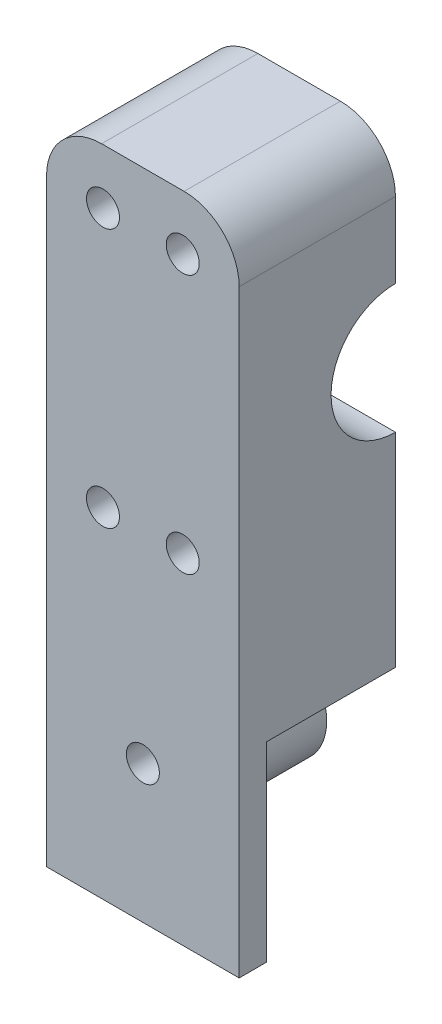
SolidWorks part; units mm, degrees
material "Nylon 6/10"
ref_plane "Front Plane" through (0, 0, 0) normal (0, 0, 1) x (1, 0, 0)
ref_plane "Top Plane" through (0, 0, 0) normal (0, 1, 0) x (1, 0, 0)
ref_plane "Right Plane" through (0, 0, 0) normal (1, 0, 0) x (0, 0, -1)
sketch "Sketch1" plane through (0, 0, 0) normal (1, 0, 0) x (0, 0, -1)
  line L1 (-28.4, -59.4) -> (-23.4, -59.4)
  line L2 (-28.4, -59.4) -> (-28.4, 59.4) construction
  line L3 (-28.4, 59.4) -> (28.4, 59.4)
  line L4 (28.4, -59.4) -> (28.4, 59.4) construction
  line L5 (-28.4, -59.4) -> (28.4, 59.4) construction
  line L6 (-28.4, 59.4) -> (28.4, -59.4) construction
  line L7 (28.4, 59.4) -> (28.4, -59.4)
  line L8 (-28.4, 59.4) -> (-28.4, -59.4)
  line L9 (-28.4, -14.4) -> (28.4, -14.4) construction
  line L10 (23.4, -59.4) -> (28.4, -59.4)
  line L11 (-23.4, -14.4) -> (23.4, -14.4)
  line L12 (-23.4, -14.4) -> (-23.4, -59.4)
  line L14 (23.4, -14.4) -> (23.4, -59.4)
  circle A0 centre (0, 24) radius 12.7 construction
  circle A1 centre (0, 24) radius 11.7
  point P0 (0, 0)
  dimension "D3" = 25.4
  dimension "D7" = 5
  dimension "D2" = 73.8
  dimension "D8" = 1
  dimension "D1" = 56.8
  dimension "D4" = 35.4
  dimension "D5" = 45
  dimension "D6" = 5
extrude "Boss-Extrude1" add sketch "Sketch1" along normal blind 35
sketch "Sketch2" plane through (0, 0, 28.4) normal (0, 0, 1) x (1, 0, 0)
  line L0 (35, -59.4) -> (0, -59.4) construction
  line L1 (0, -14.4) -> (35, -14.4) construction
  line L3 (0, -24.7175) -> (0, -13.4)
  line L4 (0, -59.4) -> (0, 59.4) construction
  line L6 (35, 59.4) -> (35, -59.4) construction
  line L7 (35, -13.4) -> (35, -24.7175)
  line L8 (0, -13.4) -> (35, -13.4)
  line L9 (0, 59.4) -> (0, -59.4) construction
  circle A0 centre (17.5, -34.4) radius 10
  arc A3 (35, -24.7175) -> (0, -24.7175) centre (17.5, -34.4) ccw
  point P4 (17.5, -59.4)
  dimension "D1" = 20
  dimension "D2" = 20
  dimension "D3" = 1
extrude "Boss-Extrude3" add sketch "Sketch2" against normal up to surface (51.8 mm away) up to face at (17.5, -36.9, -23.4)
sketch "Sketch3" plane through (0, 0, 28.4) normal (0, 0, 1) x (1, 0, 0)
  line L0 (0, 59.4) -> (0, -59.4) construction
  line L1 (35, 59.4) -> (0, 59.4) construction
  line L2 (35, 59.4) -> (35, -59.4) construction
  circle A0 centre (10.25, 49.4) radius 3
  circle A1 centre (17.5, -34.4) radius 3
  circle A2 centre (10.25, 2.3) radius 3
  circle A3 centre (24.75, 2.3) radius 3
  circle A4 centre (24.75, 49.4) radius 3
  dimension "D1" = 6
  dimension "D2" = 10
  dimension "D5" = 47.1
  dimension "D3" = 10.25
  dimension "D4" = 10.25
extrude "Cut-Extrude1" cut sketch "Sketch3" against normal through all both and the other way through all
ref_plane "Plane2" through (12.7375, 0, 0) normal (-1, 0, 0) x (0, 0, 1)
sketch "Sketch6" plane through (35, 0, 0) normal (1, 0, 0) x (0, 0, -1)
  line L0 (28.4, 59.4) -> (-28.4, 59.4) construction
  line L1 (0, 59.4) -> (28.4, 59.4)
  line L2 (0, 59.4) -> (0, -59.4)
  line L3 (0, -59.4) -> (28.4, -59.4)
  line L4 (28.4, 59.4) -> (28.4, -59.4)
extrude "Cut-Extrude3" cut sketch "Sketch6" against normal through all
sketch "Sketch7" plane through (0, 0, 0) normal (0, 0, -1) x (-1, 0, 0)
  line L0 (0, 59.4) -> (-35, 59.4) construction
  line L1 (-35, 59.4) -> (-35, 35.7) construction
  line L2 (0, 12.3) -> (-35, 12.3) construction
  circle A0 centre (-24.75, 49.4) radius 4
  circle A1 centre (-10.25, 49.4) radius 4
  circle A2 centre (-24.75, 2.3) radius 4
  circle A3 centre (-10.25, 2.3) radius 4
  circle A7 centre (-24.75, 49.4) radius 3
  circle A8 centre (-10.25, 49.4) radius 3
  circle A9 centre (-10.25, 2.3) radius 3
  circle A10 centre (-24.75, 2.3) radius 3
  dimension "D1" = 14.5
  dimension "D3" = 8
  dimension "D4" = 6
  dimension "D6" = 10
  dimension "D2" = 10
  dimension "D5" = 10.25
  dimension "D7" = 14.5
sketch "Sketch8" plane through (0, 0, 0) normal (0, 0, -1) x (-1, 0, 0)
  circle A0 centre (-17.5, -34.4) radius 10
  circle A1 centre (-17.5, -34.4) radius 3
  circle A2 centre (-17.5, -34.4) radius 10 construction
  circle A3 centre (-17.5, -34.4) radius 3 construction
extrude "Cut-Extrude4" cut sketch "Sketch8" against normal blind 5
extrude "Cut-Extrude5" cut sketch "Sketch7" against normal blind 5
fillet "Fillet1" radius 10 2 edges at (35, 59.4, 14.2) (0, 59.4, 14.2)
equation "\"keelOutDiameter\"= 1in"
equation "\"keelInDiameter\"= \"keelOutDiameter\" - 0.125in"
equation "\"frontBoltClearance\"= 7.25mm"
equation "\"betweenBoltsDistance\"= 20mm"
equation "\"wingLength\"= 1.4m"
equation "\"frontTubeLength\"= \"wingLength\" / sin ( 34.95deg )"
equation "\"plateThickness\"= 5mm"
equation "\"crossBarOutDiameter\"= 1in"
equation "\"crossBarInDiameter\"= \"crossBarOutDiameter\" - 0.125in"
equation "\"frontToCrossBar\"= 466mm"
equation "\"D3@Sketch1\"=\"keelOutDiameter\""
